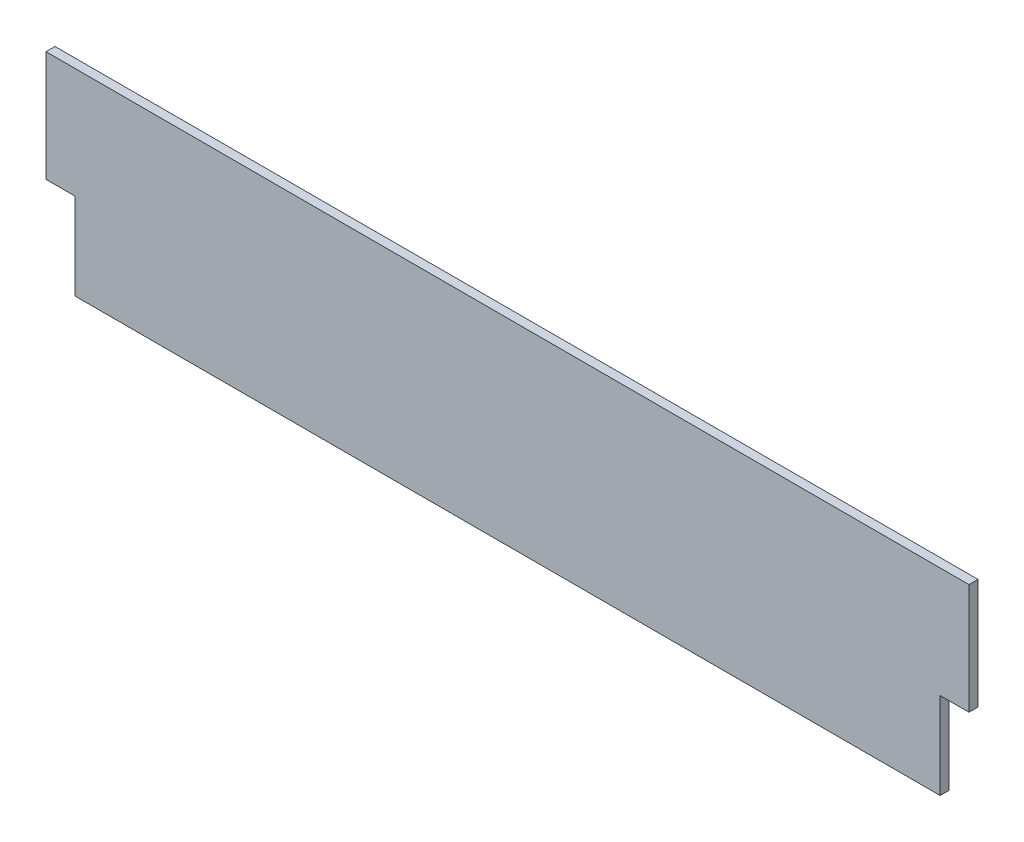
SolidWorks part; units mm, degrees
material "Pine"
ref_plane "Front Plane" through (0, 0, 0) normal (0, 0, 1) x (1, 0, 0)
ref_plane "Top Plane" through (0, 0, 0) normal (0, 1, 0) x (1, 0, 0)
ref_plane "Right Plane" through (0, 0, 0) normal (1, 0, 0) x (0, 0, -1)
sketch "Sketch1" plane through (0, 0, 0) normal (0, 0, 1) x (1, 0, 0)
  line L0 (622.3537, -57.15) -> (622.3537, 31.75) construction
  line L1 (50.8537, -57.15) -> (1193.8537, -57.15)
  line L2 (12.7537, 57.15) -> (12.7537, 203.2)
  line L3 (12.7537, 203.2) -> (1231.9537, 203.2)
  line L4 (1231.9537, 57.15) -> (1231.9537, 203.2)
  line L7 (12.7537, 57.15) -> (50.8537, 57.15)
  line L8 (50.8537, -57.15) -> (50.8537, 57.15)
  line L12 (1231.9537, 57.15) -> (1193.8537, 57.15)
  line L13 (1193.8537, -57.15) -> (1193.8537, 57.15)
  dimension "D1" = 260.35
  dimension "D2" = 1219.2
  dimension "D3" = 38.1
  dimension "D4" = 114.3
  dimension "D5" = 114.3
  dimension "D6" = 38.1
extrude "Boss-Extrude1" add sketch "Sketch1" along normal blind 11.9062
